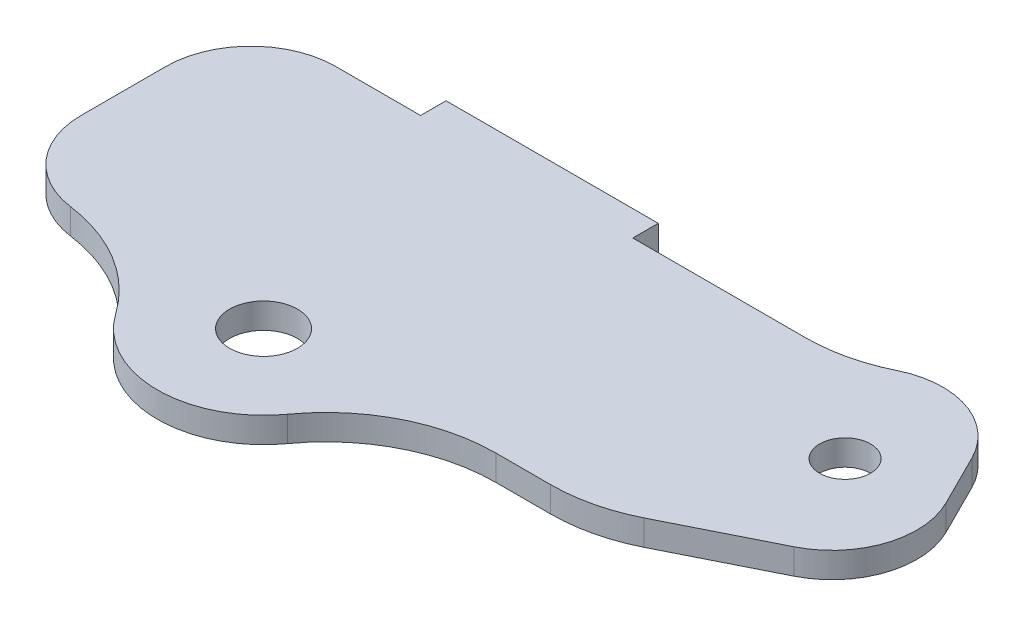
SolidWorks part; units mm, degrees
ref_plane "Front Plane" through (0, 0, 0) normal (0, 0, 1) x (1, 0, 0)
ref_plane "Top Plane" through (0, 0, 0) normal (0, 1, 0) x (1, 0, 0)
ref_plane "Right Plane" through (0, 0, 0) normal (1, 0, 0) x (0, 0, -1)
sketch "Sketch1" plane through (0, 0, 0) normal (0, 1, 0) x (1, 0, 0)
  line L0 (35, 15) -> (47.9443, 21.4721)
  line L1 (-35, 15) -> (35, 15)
  line L2 (-35, 15) -> (-35, -15)
  line L3 (-35, -15) -> (35, -15)
  line L4 (35, 15) -> (35, -15) construction
  line L5 (-35, 15) -> (35, -15) construction
  line L6 (-35, -15) -> (35, 15) construction
  line L7 (47.9443, 21.4721) -> (59.9443, -2.5279)
  line L8 (59.9443, -2.5279) -> (35, -15)
  line L9 (45, 5) -> (53.9443, 9.4721) construction
  line L10 (-15, -15) -> (10, -15)
  line L11 (-15, -15) -> (-15, -16)
  line L12 (-15, -16) -> (10, -16) construction
  line L13 (10, -15) -> (10, -16)
  line L15 (-15, 15) -> (10, 15)
  line L16 (-15, 15) -> (-15, 12)
  line L17 (-15, 12) -> (10, 12)
  line L18 (10, 15) -> (10, 12)
  line L19 (-15, 15) -> (10, 15)
  line L20 (-15, 15) -> (-15, 18)
  line L21 (-15, 18) -> (10, 18)
  line L22 (10, 15) -> (10, 18)
  arc A0 (10, -16) -> (-15, -16) centre (-2.5, -16) cw
  circle A1 centre (-2.5, -16) radius 4
  circle A2 centre (45, 5) radius 3
  point P0 (0, 0)
  point P6 (35, 0)
  point P9 (53.9443, 9.4721)
  dimension "D8" = 8
  dimension "D10" = 6
  dimension "D1" = 30
  dimension "D2" = 70
  dimension "D3" = 10
  dimension "D4" = 5
  dimension "D5" = 1
  dimension "D6" = 25
  dimension "D7" = 20
  dimension "D9" = 10
  dimension "D11" = 25
  dimension "D12" = 3
  dimension "D13" = 20
  dimension "D14" = 3
extrude "Boss-Extrude1" add sketch "Sketch1" along normal blind 3
fillet "Fillet1" radius 10 4 edges at (-35, 1.5, 15) (-35, 1.5, -15) (59.9443, 1.5, 2.5279) (47.9443, 1.5, -21.4721)
fillet "Fillet2" radius 20 4 edges at (35, 1.5, -15) (35, 1.5, 15) (10, 1.5, 15) (-15, 1.5, 15)
